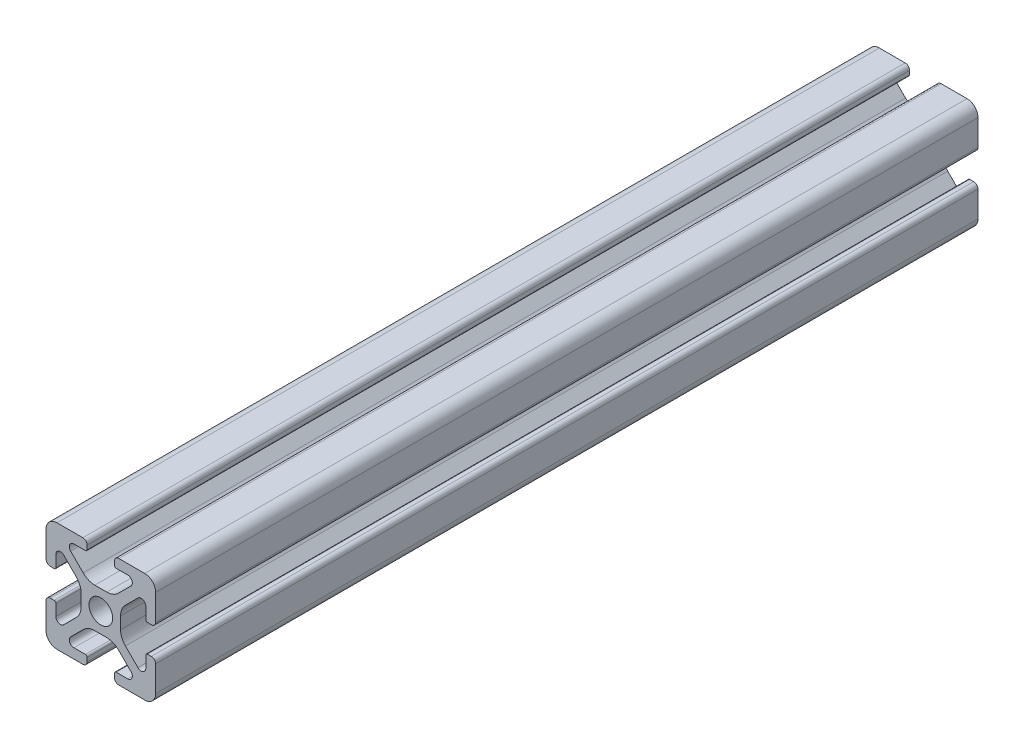
SolidWorks part; units mm, degrees
ref_plane "Front Plane" through (0, 0, 0) normal (0, 0, 1) x (1, 0, 0)
ref_plane "Top Plane" through (0, 0, 0) normal (0, 1, 0) x (1, 0, 0)
ref_plane "Right Plane" through (0, 0, 0) normal (1, 0, 0) x (0, 0, -1)
sketch "Sketch1" plane through (0, 0, 0) normal (0, 0, 1) x (1, 0, 0)
  line L0 (0, 10) -> (0, -10) construction
  line L1 (10, 0) -> (-10, 0) construction
  line L2 (-2.5, 10) -> (2.5, 10) construction
  line L3 (-5.75, 8.2) -> (5.75, 8.2) construction
  circle A0 centre (0, 0) radius 2.15 construction
  point P4 (0, 0)
  point P8 (0, 0)
  point P10 (0, 3.6)
  point P14 (0, 10)
  point P17 (0, 8.2)
  dimension "Thru Hole" = 4.3
  dimension "Height" = 20
  dimension "T Slot Depth" = 6.4
  dimension "T Slot Top Width" = 5
  dimension "T Slot Max Width" = 11.5
  dimension "Wall" = 1.8
sketch "Sketch2" plane through (0, 0, 0) normal (1, 0, 0) x (0, 0, -1)
  line L0 (152.4, 0) -> (-152.4, 0) construction
  point P4 (0, 0)
  dimension "D1" = 304.8
sketch "Sketch3" plane through (0, 0, 0) normal (0, 0, 1) x (1, 0, 0)
  line L0 (3.2874, 10) -> (8, 10)
  line L1 (10, 8) -> (10, -8) construction
  line L2 (8, -10) -> (-8, -10) construction
  line L3 (-10, 10) -> (10, -10) construction
  line L4 (2.5, 9.2126) -> (2.5, 8.5048)
  line L5 (-5.75, 8.2) -> (5.75, 8.2) construction
  line L6 (2.8048, 8.2) -> (4.9118, 8.2)
  line L7 (5.5045, 6.7691) -> (3.2141, 4.4787)
  line L8 (1.0928, 3.6) -> (-1.0928, 3.6)
  line L9 (0, 10) -> (0, -10) construction
  line L10 (5.75, 8.2) -> (5.75, 0) construction
  line L11 (10, 0) -> (-10, 0) construction
  line L12 (0, 0) -> (0, 10) construction
  line L13 (-2.5, 9.2126) -> (-2.5, 8.5048)
  line L14 (-5.5045, 6.7691) -> (-3.2141, 4.4787)
  line L15 (-2.8048, 8.2) -> (-4.9118, 8.2)
  line L16 (-3.2874, 10) -> (-8, 10)
  line L17 (0, 0) -> (-10, 0) construction
  line L18 (-10, 3.2874) -> (-10, 8)
  line L19 (-8.2, 2.8048) -> (-8.2, 4.9118)
  line L20 (-6.7691, 5.5045) -> (-4.4787, 3.2141)
  line L21 (-9.2126, 2.5) -> (-8.5048, 2.5)
  line L22 (-3.6, -1.0928) -> (-3.6, 1.0928)
  line L23 (-6.7691, -5.5045) -> (-4.4787, -3.2141)
  line L24 (-8.2, -2.8048) -> (-8.2, -4.9118)
  line L25 (-9.2126, -2.5) -> (-8.5048, -2.5)
  line L26 (-10, -3.2874) -> (-10, -8)
  line L27 (9.2126, -2.5) -> (8.5048, -2.5)
  line L28 (8.2, -2.8048) -> (8.2, -4.9118)
  line L29 (6.7691, -5.5045) -> (4.4787, -3.2141)
  line L30 (3.6, -1.0928) -> (3.6, 1.0928)
  line L31 (9.2126, 2.5) -> (8.5048, 2.5)
  line L32 (6.7691, 5.5045) -> (4.4787, 3.2141)
  line L33 (8.2, 2.8048) -> (8.2, 4.9118)
  line L34 (10, 8) -> (10, 3.2874)
  line L35 (10, -3.2874) -> (10, -8)
  line L36 (3.2874, -10) -> (8, -10)
  line L37 (-3.2874, -10) -> (-8, -10)
  line L38 (-6.7691, -5.5045) -> (-4.4787, -3.2141)
  line L39 (-2.8048, -8.2) -> (-4.9118, -8.2)
  line L40 (-5.5045, -6.7691) -> (-3.2141, -4.4787)
  line L41 (-2.5, -9.2126) -> (-2.5, -8.5048)
  line L42 (1.0928, -3.6) -> (-1.0928, -3.6)
  line L43 (5.5045, -6.7691) -> (3.2141, -4.4787)
  line L44 (2.8048, -8.2) -> (4.9118, -8.2)
  line L45 (2.5, -9.2126) -> (2.5, -8.5048)
  arc A0 (4.9118, 8.2) -> (5.5045, 6.7691) centre (4.9118, 7.3618) cw
  arc A1 (3.2141, 4.4787) -> (1.0928, 3.6) centre (1.0928, 6.6) cw
  circle A2 centre (0, 0) radius 2.15 construction
  circle A3 centre (0, 0) radius 2.15
  arc A4 (3.2874, 10) -> (2.5, 9.2126) centre (3.2874, 9.2126) ccw
  arc A5 (2.5, 8.5048) -> (2.8048, 8.2) centre (2.8048, 8.5048) ccw
  arc A6 (-3.2874, 10) -> (-2.5, 9.2126) centre (-3.2874, 9.2126) cw
  arc A7 (-4.9118, 8.2) -> (-5.5045, 6.7691) centre (-4.9118, 7.3618) ccw
  arc A8 (-3.2141, 4.4787) -> (-1.0928, 3.6) centre (-1.0928, 6.6) ccw
  arc A9 (-2.5, 8.5048) -> (-2.8048, 8.2) centre (-2.8048, 8.5048) cw
  arc A10 (-8.5048, 2.5) -> (-8.2, 2.8048) centre (-8.5048, 2.8048) ccw
  arc A11 (-4.4787, 3.2141) -> (-3.6, 1.0928) centre (-6.6, 1.0928) cw
  arc A12 (-8.2, 4.9118) -> (-6.7691, 5.5045) centre (-7.3618, 4.9118) cw
  arc A13 (-10, 3.2874) -> (-9.2126, 2.5) centre (-9.2126, 3.2874) ccw
  arc A14 (-8.5048, -2.5) -> (-8.2, -2.8048) centre (-8.5048, -2.8048) cw
  arc A15 (-10, -3.2874) -> (-9.2126, -2.5) centre (-9.2126, -3.2874) cw
  arc A16 (-4.4787, -3.2141) -> (-3.6, -1.0928) centre (-6.6, -1.0928) ccw
  arc A17 (-8.2, -4.9118) -> (-6.7691, -5.5045) centre (-7.3618, -4.9118) ccw
  arc A26 (-8, -10) -> (-10, -8) centre (-8, -8) cw
  arc A27 (-8, 10) -> (-10, 8) centre (-8, 8) ccw
  arc A28 (8, 10) -> (10, 8) centre (8, 8) cw
  arc A29 (10, -8) -> (8, -10) centre (8, -8) cw
  arc A30 (8.2, -4.9118) -> (6.7691, -5.5045) centre (7.3618, -4.9118) cw
  arc A31 (4.4787, -3.2141) -> (3.6, -1.0928) centre (6.6, -1.0928) cw
  arc A32 (10, -3.2874) -> (9.2126, -2.5) centre (9.2126, -3.2874) ccw
  arc A33 (8.5048, -2.5) -> (8.2, -2.8048) centre (8.5048, -2.8048) ccw
  arc A34 (10, 3.2874) -> (9.2126, 2.5) centre (9.2126, 3.2874) cw
  arc A35 (8.2, 4.9118) -> (6.7691, 5.5045) centre (7.3618, 4.9118) ccw
  arc A36 (4.4787, 3.2141) -> (3.6, 1.0928) centre (6.6, 1.0928) ccw
  arc A37 (8.5048, 2.5) -> (8.2, 2.8048) centre (8.5048, 2.8048) cw
  arc A38 (-2.5, -8.5048) -> (-2.8048, -8.2) centre (-2.8048, -8.5048) ccw
  arc A39 (-3.2141, -4.4787) -> (-1.0928, -3.6) centre (-1.0928, -6.6) cw
  arc A40 (-4.9118, -8.2) -> (-5.5045, -6.7691) centre (-4.9118, -7.3618) cw
  arc A41 (-3.2874, -10) -> (-2.5, -9.2126) centre (-3.2874, -9.2126) ccw
  arc A42 (2.5, -8.5048) -> (2.8048, -8.2) centre (2.8048, -8.5048) cw
  arc A43 (3.2874, -10) -> (2.5, -9.2126) centre (3.2874, -9.2126) cw
  arc A44 (3.2141, -4.4787) -> (1.0928, -3.6) centre (1.0928, -6.6) ccw
  arc A45 (4.9118, -8.2) -> (5.5045, -6.7691) centre (4.9118, -7.3618) ccw
  point P36 (2.5, 10)
  point P39 (2.5, 8.2)
  point P49 (0, 3.6)
  point P77 (-3.6, 0)
  point P78 (-8.2, -2.5)
  point P79 (-10, -2.5)
  point P104 (-10, -10)
  point P110 (10, 10)
  point P114 (10, -2.5)
  point P115 (8.2, -2.5)
  point P116 (3.6, 0)
  point P141 (0, -3.6)
  dimension "D1" = 3
  dimension "D2" = 0.8382
  dimension "D4" = 0.7874
  dimension "D5" = 0.3048
  dimension "D6" = 2
  dimension "D3" = 45
extrude "Boss-Extrude1" add sketch "Sketch3" along normal blind 150 contours A45 L44 A42 L45 A43 L36 A29 L35 A32 L27 A33 L28 A30 L29 A31 L30 A36 L32 A35 L33 A37 L31 A34 L34 A28 L0 A4 L4 A5 L6 A0 L7 A1 L8 A8 L14 A7 L15 A9 L13 A6 L16 A27 L18 A13 L21 A10 L19 A12 L20 A11
